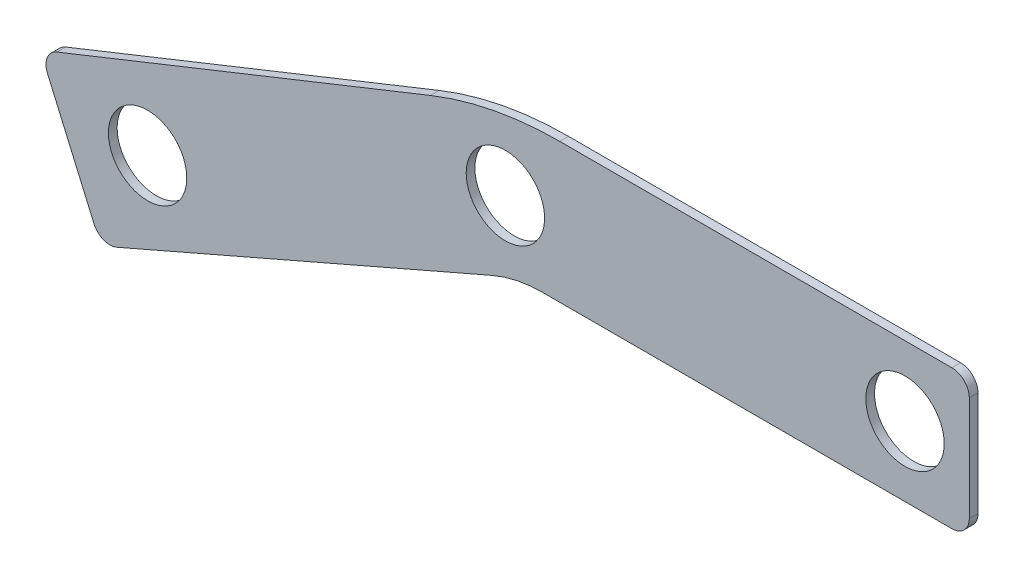
SolidWorks part; units mm, degrees
ref_plane "Front Plane" through (0, 0, 0) normal (0, 0, 1) x (1, 0, 0)
ref_plane "Top Plane" through (0, 0, 0) normal (0, 1, 0) x (1, 0, 0)
ref_plane "Right Plane" through (0, 0, 0) normal (1, 0, 0) x (0, 0, -1)
sketch "Sketch1" plane through (0, 0, 0) normal (0, 0, 1) x (1, 0, 0)
  line L0 (0, 0) -> (165.1, 0)
  line L1 (0, 0) -> (-151.3937, -65.8631)
  line L2 (165.1, 0) -> (165.1, 50.8)
  line L3 (165.1, 50.8) -> (-8.5783, 50.8)
  line L4 (-151.3937, -65.8631) -> (-173.494, -15.0631)
  line L5 (-173.494, -15.0631) -> (-8.5783, 50.8)
  point P3 (0, 0)
  point P8 (-8.5783, 50.8)
  dimension "D1" = 165.1
  dimension "D2" = 165.1
  dimension "D3" = 50.8
  dimension "D4" = 50.8
extrude "Boss-Extrude1" add sketch "Sketch1" along normal blind 3.175
fillet "Fillet1" radius 45.72 1 edges at (0, 0, 1.5875)
fillet "Fillet4" radius 127 1 edges at (-8.5783, 50.8, 1.5875)
fillet "Fillet5" radius 6.35 1 edges at (-151.3937, -65.8631, 1.5875)
fillet "Fillet6" radius 6.35 1 edges at (-173.494, -15.0631, 1.5875)
fillet "Fillet7" radius 6.35 1 edges at (165.1, 0, 1.5875)
fillet "Fillet8" radius 6.35 1 edges at (165.1, 50.8, 1.5875)
sketch "Sketch4" plane through (0, 0, 0) normal (0, 0, -1) x (-1, 0, 0)
  circle A0 centre (-141.6744, 25.4) radius 14.2875
  circle A1 centre (134.3692, -28.767) radius 14.2875
  circle A2 centre (3.9697, 23.778) radius 14.2875
  dimension "D1" = 28.575
  dimension "D2" = 28.575
  dimension "D3" = 28.575
extrude "Cut-Extrude1" cut sketch "Sketch4" against normal blind 18.415
